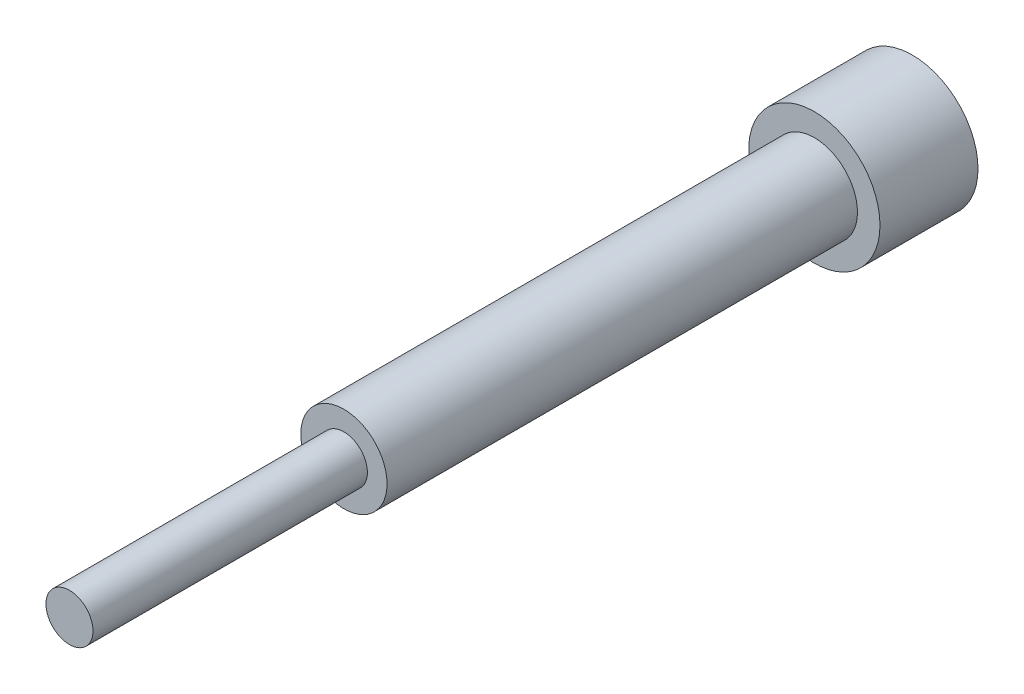
SolidWorks part; units mm, degrees
ref_plane "Alzado" through (0, 0, 0) normal (0, 0, 1) x (1, 0, 0)
ref_plane "Planta" through (0, 0, 0) normal (0, 1, 0) x (1, 0, 0)
ref_plane "Vista lateral" through (0, 0, 0) normal (1, 0, 0) x (0, 0, -1)
sketch "Croquis1" plane through (0, 0, 0) normal (0, 0, 1) x (1, 0, 0)
  circle A0 centre (0, 0) radius 16.75
  dimension "D1" = 33.5
extrude "Saliente-Extruir1" add sketch "Croquis1" along normal blind 25
sketch "Croquis2" plane through (0, 0, 25) normal (0, 0, 1) x (1, 0, 0)
  circle A0 centre (0, 0) radius 11
  dimension "D1" = 22
extrude "Saliente-Extruir3" add sketch "Croquis2" along normal blind 120
sketch "Croquis3" plane through (0, 0, 145) normal (0, 0, 1) x (1, 0, 0)
  circle A0 centre (0, 0) radius 6
  dimension "12" = 12
extrude "Saliente-Extruir4" add sketch "Croquis3" along normal blind 70
